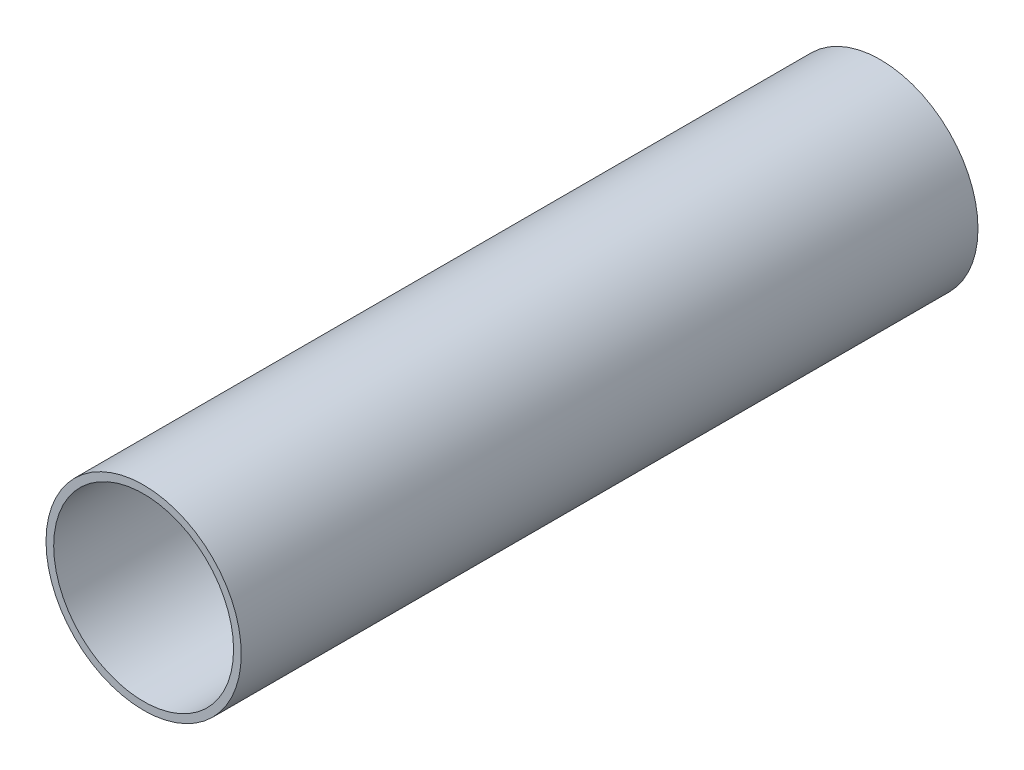
SolidWorks part; units mm, degrees
ref_plane "Front Plane" through (0, 0, 0) normal (0, 0, 1) x (1, 0, 0)
ref_plane "Top Plane" through (0, 0, 0) normal (0, 1, 0) x (1, 0, 0)
ref_plane "Right Plane" through (0, 0, 0) normal (1, 0, 0) x (0, 0, -1)
sketch "Sketch1" plane through (0, 0, 0) normal (0, 0, 1) x (1, 0, 0)
  circle A0 centre (0, 0) radius 15.9
  circle A1 centre (0, 0) radius 14.65
  dimension "D1" = 31.8
  dimension "D2" = 29.3
extrude "Boss-Extrude1" add sketch "Sketch1" against normal blind 120
